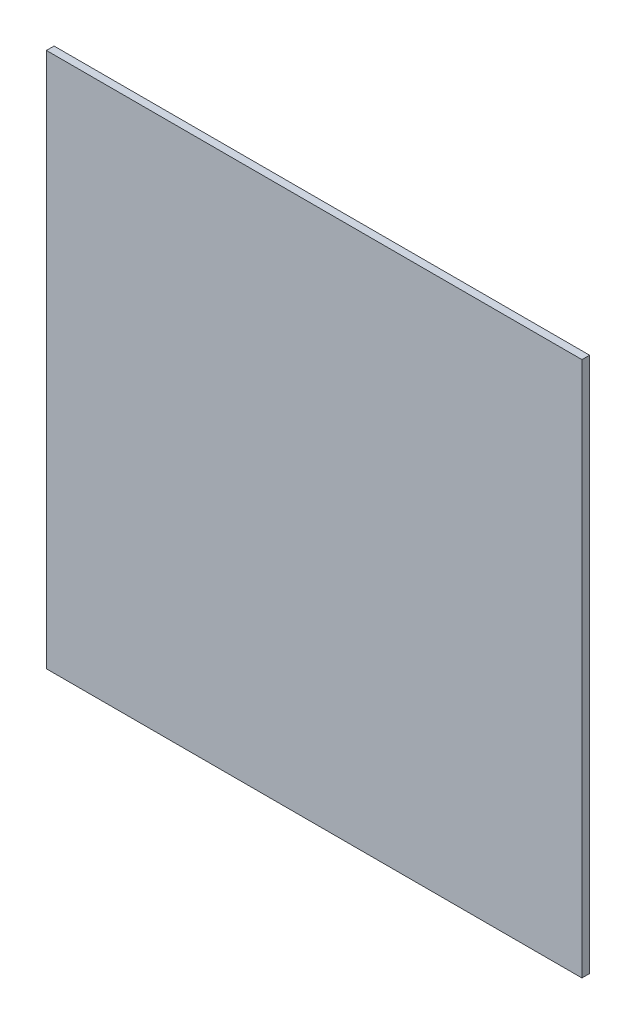
SolidWorks part; units mm, degrees
ref_plane "Alzado" through (0, 0, 0) normal (0, 0, 1) x (1, 0, 0)
ref_plane "Planta" through (0, 0, 0) normal (0, 1, 0) x (1, 0, 0)
ref_plane "Vista lateral" through (0, 0, 0) normal (1, 0, 0) x (0, 0, -1)
sketch "Croquis1" plane through (0, 0, 0) normal (0, 0, 1) x (1, 0, 0)
  line L1 (-62.4441, 24.485) -> (7.5559, 24.485)
  line L2 (-62.4441, 24.485) -> (-62.4441, -45.515)
  line L3 (-62.4441, -45.515) -> (7.5559, -45.515)
  line L4 (7.5559, 24.485) -> (7.5559, -45.515)
  dimension "D1" = 70
  dimension "D2" = 70
extrude "Saliente-Extruir1" add sketch "Croquis1" along normal blind 1
